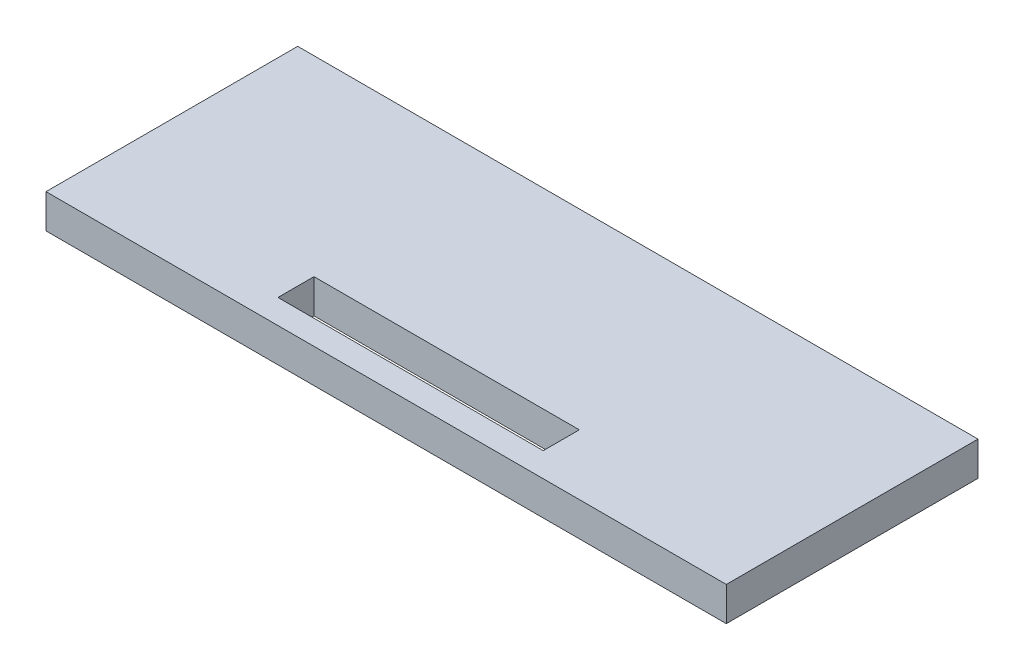
SolidWorks part; units mm, degrees
ref_plane "Alzado" through (0, 0, 0) normal (0, 0, 1) x (1, 0, 0)
ref_plane "Planta" through (0, 0, 0) normal (0, 1, 0) x (1, 0, 0)
ref_plane "Vista lateral" through (0, 0, 0) normal (1, 0, 0) x (0, 0, -1)
sketch "Croquis1" plane through (0, 0, 0) normal (0, 0, 1) x (1, 0, 0)
  line L7 (49.9525, -86.5025) -> (49.9525, -90.5025)
  line L8 (49.9525, -90.5025) -> (-50.0475, -90.5025)
  line L9 (-50.0475, -90.5025) -> (-50.0475, -86.5025)
  line L10 (-50.0475, -86.5025) -> (49.9525, -86.5025)
extrude "Saliente-Extruir1" add sketch "Croquis1" along normal up to surface (37 mm away)
sketch "Croquis2" plane through (0, -90.5025, 0) normal (0, -1, 0) x (1, 0, 0)
  line L4 (49.9525, 0) -> (49.9525, 37)
  line L5 (49.9525, 37) -> (-50.0475, 37)
  line L6 (-50.0475, 37) -> (-50.0475, 0)
  line L7 (-50.0475, 0) -> (49.9525, 0)
  line L8 (49.9525, 0) -> (49.9525, 37)
  line L9 (49.9525, 37) -> (-50.0475, 37)
  line L10 (-50.0475, 37) -> (-50.0475, 0)
  line L11 (-50.0475, 0) -> (49.9525, 0)
  dimension "D1" = 0
extrude "Saliente-Extruir2" add sketch "Croquis2" along normal blind 1
sketch "Croquis3" plane through (0, -91.5025, 0) normal (0, -1, 0) x (1, 0, 0)
  line L2 (19.4696, 33.4244) -> (-19.5304, 33.4244)
  line L3 (-19.5304, 33.4244) -> (-19.5304, 28.1244)
  line L4 (-19.5304, 28.1244) -> (19.4696, 28.1244)
  line L5 (19.4696, 33.4244) -> (19.4696, 28.1244)
  point P8 (-0.0304, 28.1244)
extrude "Cortar-Extruir1" cut sketch "Croquis3" against normal blind 10 contours L4 L5 L2 L3
